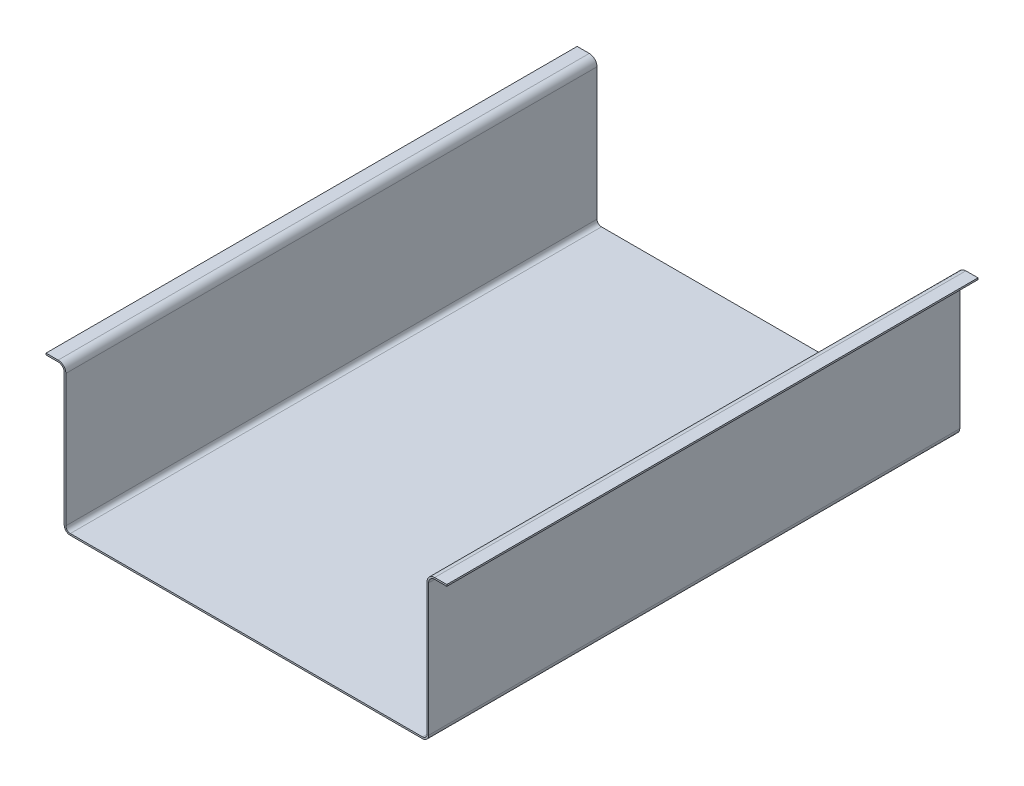
SolidWorks part; units mm, degrees
material "Plain Carbon Steel"
ref_plane "Front Plane" through (0, 0, 0) normal (0, 0, 1) x (1, 0, 0)
ref_plane "Top Plane" through (0, 0, 0) normal (0, 1, 0) x (1, 0, 0)
ref_plane "Right Plane" through (0, 0, 0) normal (1, 0, 0) x (0, 0, -1)
sketch "Sketch1" plane through (0, 0, 0) normal (0, 0, 1) x (1, 0, 0)
  line L0 (-393.7, 301.3837) -> (-419.1, 301.3837)
  line L1 (-368.3, 0) -> (368.3, 0)
  line L2 (-381, 12.7) -> (-381, 288.6837)
  line L3 (393.7, 301.3837) -> (419.1, 301.3837)
  line L4 (381, 12.7) -> (381, 288.6837)
  line L7 (393.7, 304.8) -> (419.1, 304.8)
  line L8 (377.5837, 12.7) -> (377.5837, 288.6837)
  line L9 (-368.3, 3.4163) -> (368.3, 3.4163)
  line L10 (-377.5837, 12.7) -> (-377.5837, 288.6837)
  line L11 (-393.7, 304.8) -> (-419.1, 304.8)
  line L12 (-419.1, 304.8) -> (-419.1, 301.3837)
  line L13 (419.1, 304.8) -> (419.1, 301.3837)
  line L14 (419.1, 301.3837) -> (434.3362, 301.3837)
  arc A0 (-368.3, 0) -> (-381, 12.7) centre (-368.3, 12.7) cw
  arc A1 (368.3, 0) -> (381, 12.7) centre (368.3, 12.7) ccw
  arc A2 (393.7, 301.3837) -> (381, 288.6837) centre (393.7, 288.6837) ccw
  arc A3 (-381, 288.6837) -> (-393.7, 301.3837) centre (-393.7, 288.6837) ccw
  arc A4 (393.7, 304.8) -> (377.5837, 288.6837) centre (393.7, 288.6837) ccw
  arc A5 (368.3, 3.4163) -> (377.5837, 12.7) centre (368.3, 12.7) ccw
  arc A6 (-368.3, 3.4163) -> (-377.5837, 12.7) centre (-368.3, 12.7) cw
  arc A7 (-377.5837, 288.6837) -> (-393.7, 304.8) centre (-393.7, 288.6837) ccw
  point P0 (0, 0)
  point P1 (0, 0)
  dimension "D3" = 12.7
  dimension "D5" = 12.7
  dimension "D1" = 762
  dimension "D2" = 304.8
  dimension "D4" = 38.1
  dimension "D6" = 3.4163
extrude "Base" add sketch "Sketch1" along normal mid plane 1110.7674 contours L10 A7 L11 L12 L0 A3 L2 A0 L1 A1 L4 A2 L3 L13 L7 A4 L8 A5 L9 A6
